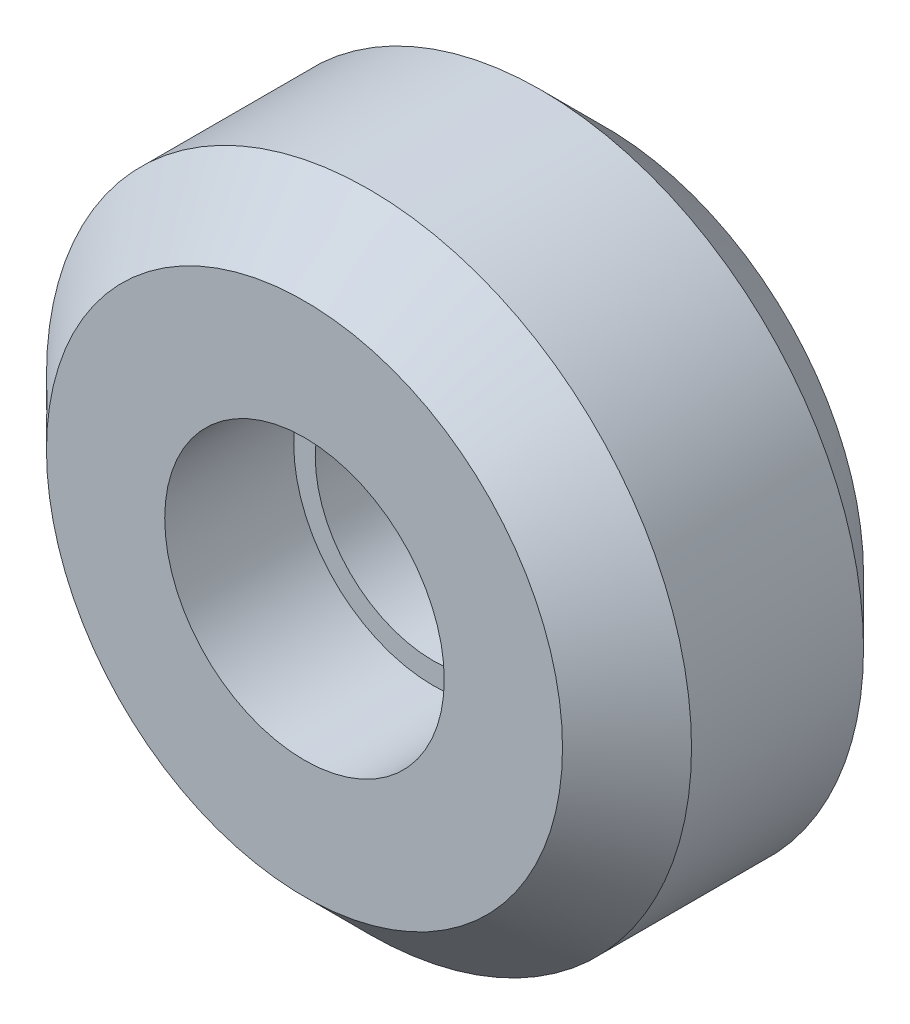
SolidWorks part; units mm, degrees
material "PVAL"
ref_plane "Front Plane" through (0, 0, 0) normal (0, 0, 1) x (1, 0, 0)
ref_plane "Top Plane" through (0, 0, 0) normal (0, 1, 0) x (1, 0, 0)
ref_plane "Right Plane" through (0, 0, 0) normal (1, 0, 0) x (0, 0, -1)
sketch "Sketch1" plane through (0, 0, 0) normal (0, 0, 1) x (1, 0, 0)
  circle A0 centre (0, 0) radius 5.5
  circle A1 centre (0, 0) radius 15
  dimension "D1" = 11
  dimension "D2" = 30
extrude "Boss-Extrude1" add sketch "Sketch1" along normal blind 8
sketch "Sketch2" plane through (0, 0, 8) normal (0, 0, 1) x (1, 0, 0)
  circle A0 centre (0, 0) radius 6.5
  circle A1 centre (0, 0) radius 15
  dimension "D1" = 13
  dimension "D2" = 30
extrude "Boss-Extrude2" add sketch "Sketch2" along normal blind 6
chamfer "Chamfer1" distance 3 angle 45 2 edges at (15, 0, 14) (15, 0, 0)
